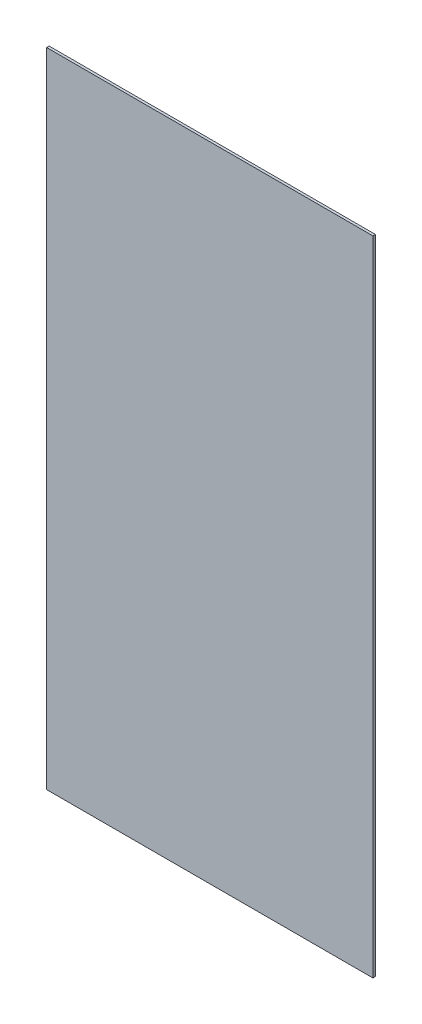
SolidWorks part; units mm, degrees
material "PVC Rigid"
ref_plane "Front Plane" through (0, 0, 0) normal (0, 0, 1) x (1, 0, 0)
ref_plane "Top Plane" through (0, 0, 0) normal (0, 1, 0) x (1, 0, 0)
ref_plane "Right Plane" through (0, 0, 0) normal (1, 0, 0) x (0, 0, -1)
sketch "Sketch1" plane through (0, 0, 0) normal (0, 0, 1) x (1, 0, 0)
  line L1 (-217.8242, 371.6427) -> (112.3758, 371.6427)
  line L2 (-217.8242, 371.6427) -> (-217.8242, -278.5973)
  line L3 (-217.8242, -278.5973) -> (112.3758, -278.5973)
  line L4 (112.3758, 371.6427) -> (112.3758, -278.5973)
  dimension "D1" = 330.2
  dimension "D2" = 650.24
extrude "Boss-Extrude1" add sketch "Sketch1" along normal blind 2.54
